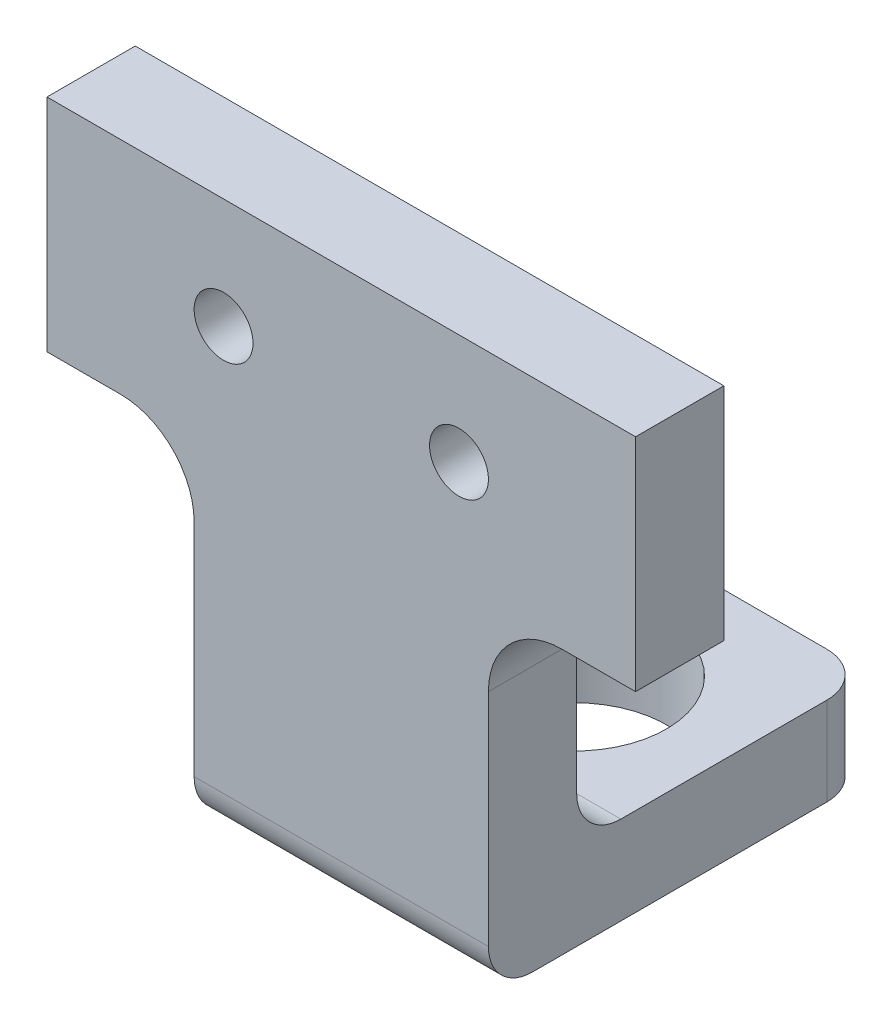
SolidWorks part; units mm, degrees
ref_plane "Front Plane" through (0, 0, 0) normal (0, 0, 1) x (1, 0, 0)
ref_plane "Top Plane" through (0, 0, 0) normal (0, 1, 0) x (1, 0, 0)
ref_plane "Right Plane" through (0, 0, 0) normal (1, 0, 0) x (0, 0, -1)
sketch "Sketch1" plane through (0, 0, 0) normal (0, 0, 1) x (1, 0, 0)
  line L0 (0, 70) -> (0, 55) construction
  line L1 (-20, 70) -> (20, 70)
  line L2 (-20, 70) -> (-20, 55)
  line L3 (-20, 55) -> (-15, 55)
  line L4 (20, 70) -> (20, 55)
  line L5 (-41.3734, 15) -> (52.0298, 15) construction
  line L6 (-10, 50) -> (-10, 32)
  line L7 (10, 50) -> (10, 32)
  line L9 (15, 55) -> (20, 55)
  line L10 (-10, 32) -> (10, 32)
  circle A0 centre (-8, 62.5) radius 2
  circle A1 centre (8, 62.5) radius 2
  arc A2 (10, 50) -> (15, 55) centre (15, 50) cw
  arc A3 (-10, 50) -> (-15, 55) centre (-15, 50) ccw
  point P19 (10, 55)
  dimension "D3" = 4
  dimension "D4" = 4
  dimension "D15" = 5
  dimension "D1" = 15
  dimension "D2" = 40
  dimension "D5" = 16
  dimension "D6" = 8
  dimension "D7" = 7.5
  dimension "D8" = 7.5
  dimension "D9" = 8
  dimension "D10" = 62.5
  dimension "D11" = 15
  dimension "D12" = 10
  dimension "D13" = 10
  dimension "D14" = 32
extrude "Boss-Extrude1" add sketch "Sketch1" along normal blind 6 contours L1 L4 L9 A2 L7 L10 L6 A3 L3 L2 | A0 | A1
sketch "Sketch2" plane through (0, 0, 0) normal (0, 0, -1) x (-1, 0, 0)
  line L0 (10, 50) -> (10, 32) construction
  line L1 (-10, 32) -> (10, 32)
  line L2 (-10, 32) -> (-10, 38)
  line L3 (-10, 38) -> (10, 38)
  line L4 (10, 32) -> (10, 38)
  dimension "D1" = 6
extrude "Boss-Extrude2" add sketch "Sketch2" along normal blind 20
sketch "Sketch3" plane through (0, 38, 0) normal (0, 1, 0) x (1, 0, 0)
  circle A0 centre (0, 9.85) radius 6.25
  dimension "D1" = 9.85
  dimension "D2" = 12.5
extrude "Cut-Extrude1" cut sketch "Sketch3" against normal blind 6
fillet "Fillet1" radius 3 2 edges at (10, 35, -20) (-10, 35, -20)
fillet "Fillet2" radius 3 1 edges at (0, 38, 0)
fillet "Fillet3" radius 3 1 edges at (0, 32, 6)
